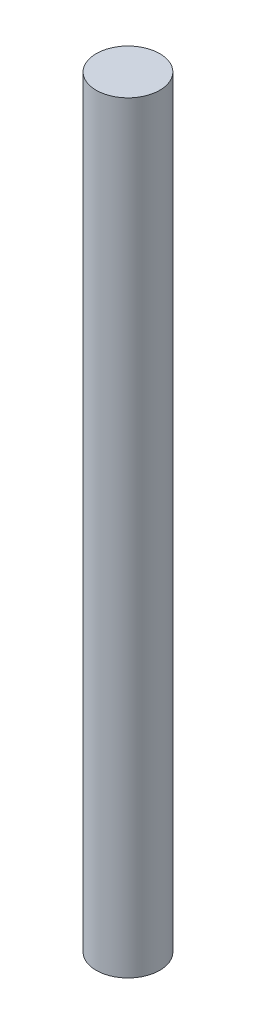
SolidWorks part; units mm, degrees
material "Oak"
ref_plane "Front Plane" through (0, 0, 0) normal (0, 0, 1) x (1, 0, 0)
ref_plane "Top Plane" through (0, 0, 0) normal (0, 1, 0) x (1, 0, 0)
ref_plane "Right Plane" through (0, 0, 0) normal (1, 0, 0) x (0, 0, -1)
other "Configuration Table"
sketch "Sketch1" plane through (0, 0, 0) normal (0, 1, 0) x (1, 0, 0)
  circle A0 centre (0, 0) radius 12.7
  dimension "D1" = 25.4
extrude "Boss-Extrude1" add sketch "Sketch1" along normal blind 304.8
